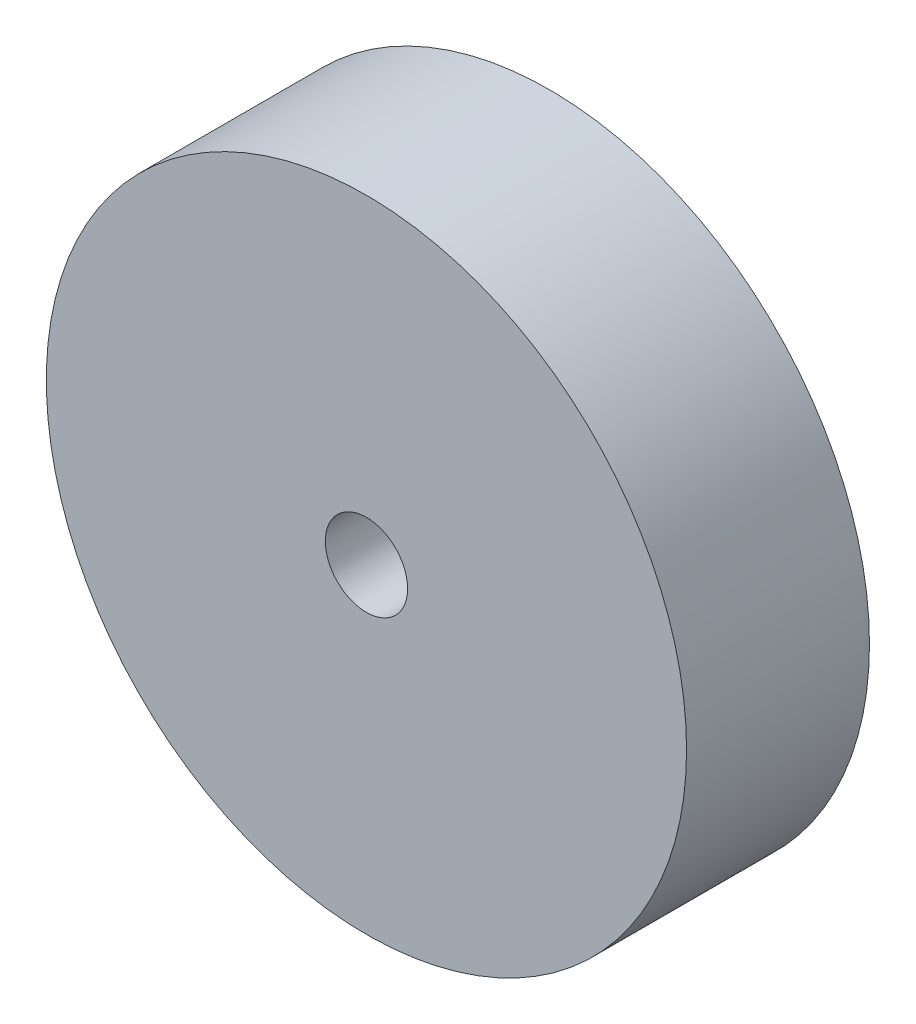
SolidWorks part; units mm, degrees
ref_plane "Front Plane" through (0, 0, 0) normal (0, 0, 1) x (1, 0, 0)
ref_plane "Top Plane" through (0, 0, 0) normal (0, 1, 0) x (1, 0, 0)
ref_plane "Right Plane" through (0, 0, 0) normal (1, 0, 0) x (0, 0, -1)
sketch "Sketch1" plane through (0, 0, 0) normal (0, 0, 1) x (1, 0, 0)
  circle A0 centre (0, 0) radius 35
  dimension "D1" = 70
extrude "Boss-Extrude1" add sketch "Sketch1" along normal blind 20
sketch "Sketch2" plane through (0, 0, 20) normal (0, 0, 1) x (1, 0, 0)
  circle A0 centre (0, 0) radius 4.5
  dimension "D1" = 9
extrude "Cut-Extrude1" cut sketch "Sketch2" against normal blind 20 contours A0
